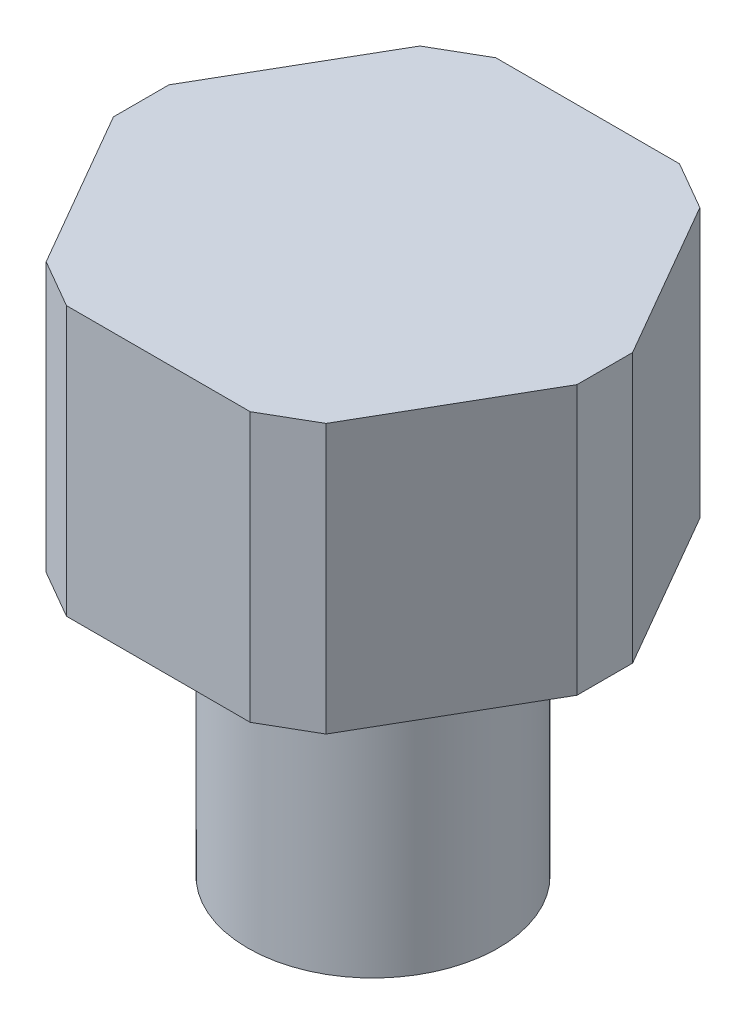
SolidWorks part; units mm, degrees
material "6061-T6 (SS)"
ref_plane "Front Plane" through (0, 0, 0) normal (0, 0, 1) x (1, 0, 0)
ref_plane "Top Plane" through (0, 0, 0) normal (0, 1, 0) x (1, 0, 0)
ref_plane "Right Plane" through (0, 0, 0) normal (1, 0, 0) x (0, 0, -1)
sketch "Sketch1" plane through (0, 0, 0) normal (0, 1, 0) x (1, 0, 0)
  circle A0 centre (0, 0) radius 5.5562
  dimension "D1" = 11.1125
extrude "Boss-Extrude1" add sketch "Sketch1" along normal blind 12.7
sketch "Sketch3" plane through (0, 12.7, 0) normal (0, 1, 0) x (1, 0, 0)
  line L0 (-5.4993, 9.525) -> (5.4993, 9.525) construction
  line L1 (5.4993, 9.525) -> (10.9985, 0) construction
  line L2 (10.9985, 0) -> (5.4993, -9.525) construction
  line L3 (5.4993, -9.525) -> (-5.4993, -9.525) construction
  line L4 (-5.4993, -9.525) -> (-10.9985, 0) construction
  line L5 (-10.9985, 0) -> (-5.4993, 9.525) construction
  line L6 (-10.287, 1.2324) -> (-10.287, -1.2324)
  line L7 (10.287, 1.2324) -> (10.287, -1.2324)
  line L8 (-6.2108, 8.2926) -> (-4.0762, 9.525)
  line L9 (4.0762, -9.525) -> (6.2108, -8.2926)
  line L10 (-6.2108, -8.2926) -> (-4.0762, -9.525)
  line L11 (4.0762, 9.525) -> (6.2108, 8.2926)
  line L12 (-10.287, 1.2324) -> (-6.2108, 8.2926)
  line L13 (-4.0762, 9.525) -> (4.0762, 9.525)
  line L14 (6.2108, 8.2926) -> (10.287, 1.2324)
  line L15 (10.287, -1.2324) -> (6.2108, -8.2926)
  line L16 (-4.0762, -9.525) -> (4.0762, -9.525)
  line L17 (-10.287, -1.2324) -> (-6.2108, -8.2926)
  point P2 (0, -9.525)
  dimension "D1" = 19.05
  dimension "D2" = 19.05
  dimension "D3" = 19.05
  dimension "D4" = 9.525
  dimension "D5" = 9.525
  dimension "D6" = 9.525
  dimension "D7" = 10.287
  dimension "D8" = 10.287
  dimension "D9" = 1.423
  dimension "D10" = 1.423
  dimension "D11" = 1.423
  dimension "D12" = 1.423
  dimension "D13" = 1.423
  dimension "D14" = 1.423
  dimension "D15" = 1.423
  dimension "D16" = 1.423
extrude "Boss-Extrude2" add sketch "Sketch3" along normal blind 11.938
